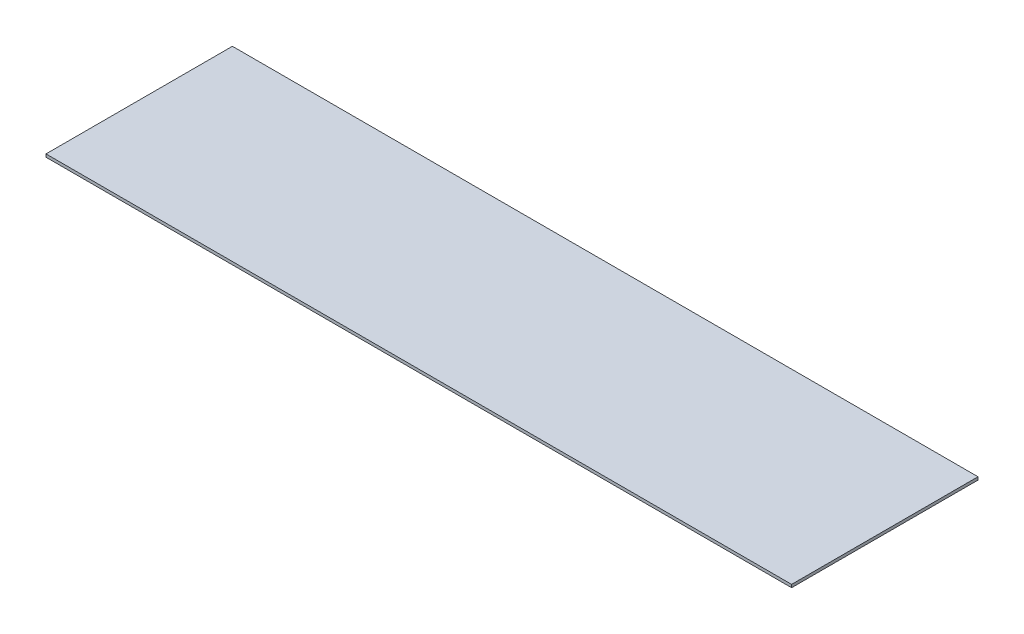
SolidWorks part; units mm, degrees
material "Nylon 101"
ref_plane "Front Plane" through (0, 0, 0) normal (0, 0, 1) x (1, 0, 0)
ref_plane "Top Plane" through (0, 0, 0) normal (0, 1, 0) x (1, 0, 0)
ref_plane "Right Plane" through (0, 0, 0) normal (1, 0, 0) x (0, 0, -1)
sketch "Sketch1" plane through (0, -80.2624, 0) normal (0, -1, 0) x (1, 0, 0)
  line L2 (0, 0) -> (406.4, 0)
  line L3 (0, 0) -> (0, 101.6)
  line L4 (0, 101.6) -> (406.4, 101.6)
  line L5 (406.4, 0) -> (406.4, 101.6)
  dimension "D2" = 406.4
  dimension "D1" = 101.6
extrude "Boss-Extrude1" add sketch "Sketch1" along normal blind 1.5875
